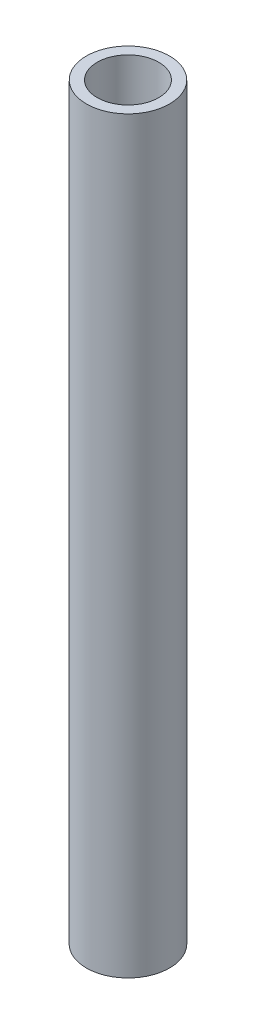
SolidWorks part; units mm, degrees
ref_plane "Front" through (0, 0, 0) normal (0, 0, 1) x (1, 0, 0)
ref_plane "Top" through (0, 0, 0) normal (0, 1, 0) x (1, 0, 0)
ref_plane "Right" through (0, 0, 0) normal (1, 0, 0) x (0, 0, -1)
sketch "Sketch1" plane through (0, 0, 0) normal (0, 1, 0) x (1, 0, 0)
  circle A0 centre (0, 0) radius 19.05
  dimension "D1" = 38.1
extrude "Boss-Extrude1" add sketch "Sketch1" along normal blind 342.9
sketch "Sketch2" plane through (0, 342.9, 0) normal (0, 1, 0) x (1, 0, 0)
  circle A0 centre (0, 0) radius 12.7
  dimension "D1" = 25.4
extrude "Cut-Extrude1" cut sketch "Sketch2" against normal through all
hole_wizard "1-1/4-7 Tapped Hole1" positions "Sketch6" profile "Sketch5" tap size "1-1/4-7" standard "ANSI Inch"
sketch "Sketch6" plane through (0, 342.9, 0) normal (0, 1, 0) x (1, 0, 0)
  point P0 (0, 0)
sketch "Sketch5" plane through (0, 342.9, 0) normal (1, 0, 0) x (0, 0, 1)
  line L0 (0, 0) -> (0, 57.4878)
  line L1 (0, 57.4878) -> (14.0894, 49.022)
  line L2 (14.0894, 49.022) -> (14.0894, 0)
  line L5 (14.0894, 0) -> (0, 0)
  line L10 (0, 57.4878) -> (-14.0894, 49.022) construction
  line L11 (0, -6.35) -> (0, 107.95) construction
  dimension "Tap Drill Dia." = 28.1788
  dimension "Tap Drill Depth" = 49.022
  dimension "Drill Angle" = 118
cosmetic thread "Hole Thread1"
hole_wizard "1-1/4-7 Tapped Hole2" positions "Sketch8" profile "Sketch7" tap size "1-1/4-7" standard "ANSI Inch"
sketch "Sketch8" plane through (0, 0, 0) normal (0, -1, 0) x (-1, 0, 0)
  point P0 (0, 0)
sketch "Sketch7" plane through (0, 0, 0) normal (1, 0, 0) x (0, 0, -1)
  line L0 (0, 0) -> (0, 57.4878)
  line L1 (0, 57.4878) -> (14.0894, 49.022)
  line L2 (14.0894, 49.022) -> (14.0894, 0)
  line L5 (14.0894, 0) -> (0, 0)
  line L10 (0, 57.4878) -> (-14.0894, 49.022) construction
  line L11 (0, -6.35) -> (0, 107.95) construction
  dimension "Tap Drill Dia." = 28.1788
  dimension "Tap Drill Depth" = 49.022
  dimension "Drill Angle" = 118
cosmetic thread "Hole Thread2"
